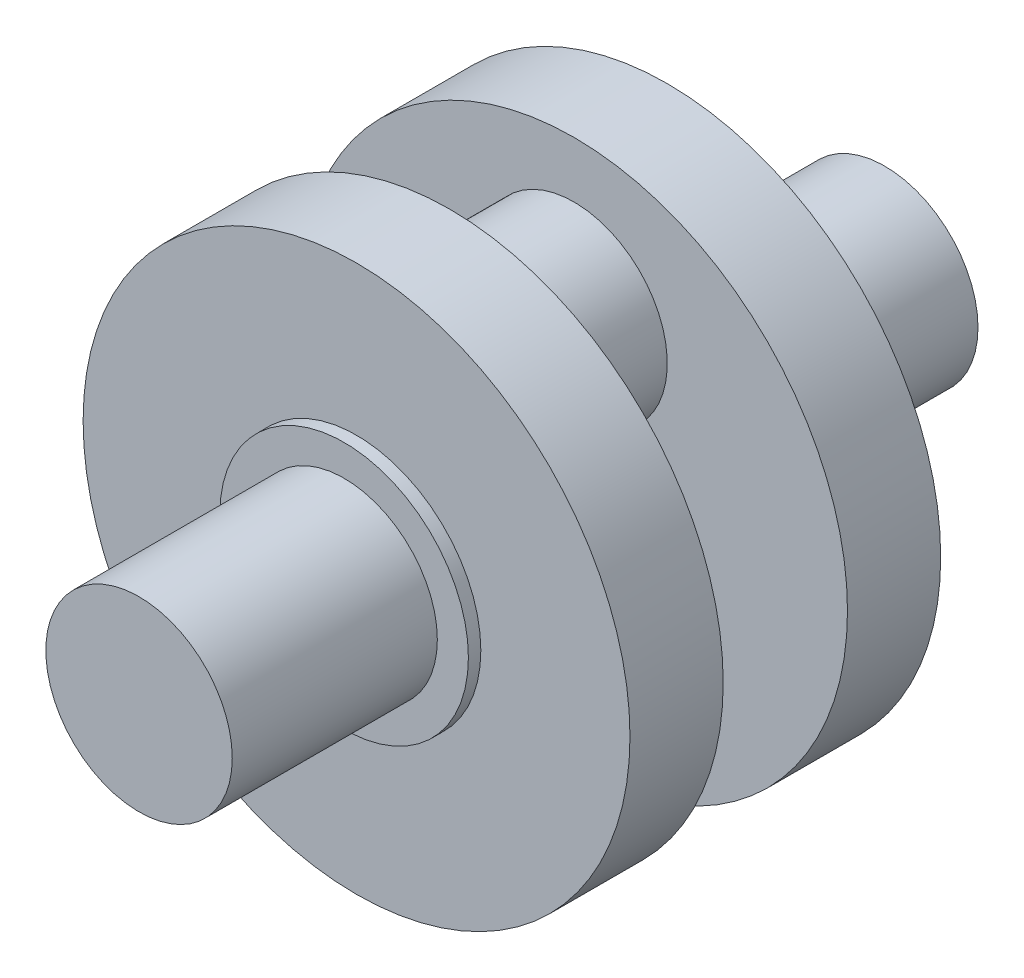
SolidWorks part; units mm, degrees
ref_plane "Front Plane" through (0, 0, 0) normal (0, 0, 1) x (1, 0, 0)
ref_plane "Top Plane" through (0, 0, 0) normal (0, 1, 0) x (1, 0, 0)
ref_plane "Right Plane" through (0, 0, 0) normal (1, 0, 0) x (0, 0, -1)
sketch "Sketch1" plane through (0, 0, 0) normal (0, 0, 1) x (1, 0, 0)
  circle A0 centre (0, 0) radius 15
  dimension "D1" = 30
extrude "Boss-Extrude1" add sketch "Sketch1" along normal blind 33
sketch "Sketch4" plane through (0, 0, 0) normal (0, 0, 1) x (1, 0, 0)
  circle A0 centre (0, 0) radius 20
  dimension "D1" = 40
extrude "Boss-Extrude3" add sketch "Sketch4" against normal blind 2
ref_plane "Plane1" through (0, 0, -2) normal (0, 0, -1) x (-1, 0, 0)
sketch "Sketch6" plane through (0, 0, -2) normal (0, 0, -1) x (-1, 0, 0)
  circle A0 centre (0, 0) radius 44
  dimension "D1" = 88
extrude "Boss-Extrude4" add sketch "Sketch6" along normal blind 15
ref_plane "Plane2" through (0, 0, -17) normal (0, 0, -1) x (-1, 0, 0)
sketch "Sketch7" plane through (0, 0, -17) normal (0, 0, -1) x (-1, 0, 0)
  circle A0 centre (0, 20) radius 15
  dimension "D2" = 30
  dimension "D1" = 20
extrude "Boss-Extrude5" add sketch "Sketch7" along normal blind 10
mirror "Mirror1" about plane through (0, 20, -27) normal (0, 0, -1) of bodies 105
